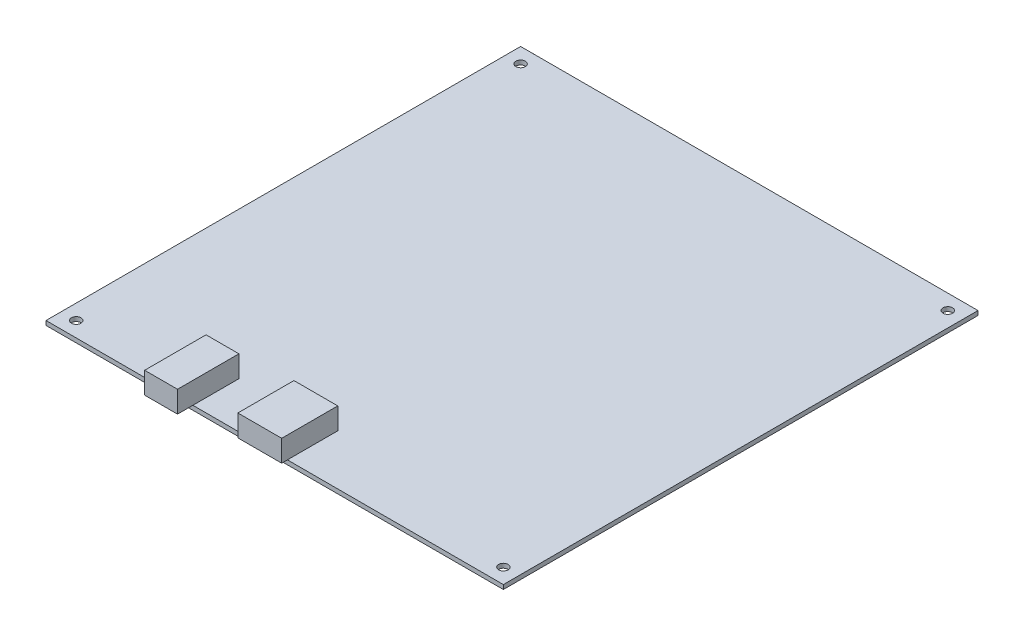
SolidWorks part; units mm, degrees
material "Copper"
ref_plane "Front Plane" through (0, 0, 0) normal (0, 0, 1) x (1, 0, 0)
ref_plane "Top Plane" through (0, 0, 0) normal (0, 1, 0) x (1, 0, 0)
ref_plane "Right Plane" through (0, 0, 0) normal (1, 0, 0) x (0, 0, -1)
sketch "Sketch1" plane through (0, 0, 0) normal (0, 1, 0) x (1, 0, 0)
  line L1 (-44.0443, 99.9438) -> (61.9557, 99.9438)
  line L2 (-44.0443, 99.9438) -> (-44.0443, -10.0562)
  line L3 (-44.0443, -10.0562) -> (61.9557, -10.0562)
  line L4 (61.9557, 99.9438) -> (61.9557, -10.0562)
  circle A0 centre (-40.5443, -6.5562) radius 1.1
  circle A1 centre (58.4557, -6.5562) radius 1.1
  circle A2 centre (-40.5443, 96.4438) radius 1.1
  circle A3 centre (58.4557, 96.4438) radius 1.1
  dimension "D3" = 2.2
  dimension "D4" = 3.5
  dimension "D6" = 3.5
  dimension "D8" = 2.2
  dimension "D11" = 2.2
  dimension "D14" = 2.2
  dimension "D1" = 110
  dimension "D2" = 106
  dimension "D5" = 3.5
  dimension "D7" = 3.5
  dimension "D9" = 3.5
  dimension "D10" = 3.5
  dimension "D12" = 3.5
  dimension "D13" = 3.5
extrude "Boss-Extrude1" add sketch "Sketch1" along normal blind 1
sketch3d "3DSketch1"
  line L0 (-44.0443, 1, 10.0562) -> (61.9557, 1, 10.0562) construction
  line L1 (-17.6243, 1, -0.6138) -> (-10.0043, 1, -0.6138)
  line L2 (-17.6243, 1, -0.6138) -> (-17.6243, 1, 13.6162)
  line L3 (-17.6243, 1, 13.6162) -> (-10.0043, 1, 13.6162)
  line L4 (-10.0043, 1, -0.6138) -> (-10.0043, 1, 13.6162)
  line L5 (-44.0443, 1, -99.9438) -> (-44.0443, 1, 10.0562) construction
  dimension "D1" = 7.62
  dimension "D2" = 10.67
  dimension "D3" = 3.56
  dimension "D4" = 26.42
extrude "Boss-Extrude3" add sketch "3DSketch1" along direction (0, 1, 0) on the side against the normal blind 5
sketch "Sketch3" plane through (0, 1, 0) normal (0, 1, 0) x (1, 0, 0)
  line L0 (-10.0043, -10.0562) -> (61.9557, -10.0562) construction
  line L1 (1.7457, 1.6138) -> (11.9057, 1.6138)
  line L2 (1.7457, 1.6138) -> (1.7457, -11.3862)
  line L3 (1.7457, -11.3862) -> (11.9057, -11.3862)
  line L4 (11.9057, 1.6138) -> (11.9057, -11.3862)
  line L5 (-10.0043, -10.0562) -> (-10.0043, 0.6138) construction
  dimension "D1" = 11.67
  dimension "D2" = 1.33
  dimension "D3" = 10.16
  dimension "D4" = 11.75
extrude "Boss-Extrude4" add sketch "Sketch3" along normal blind 5
